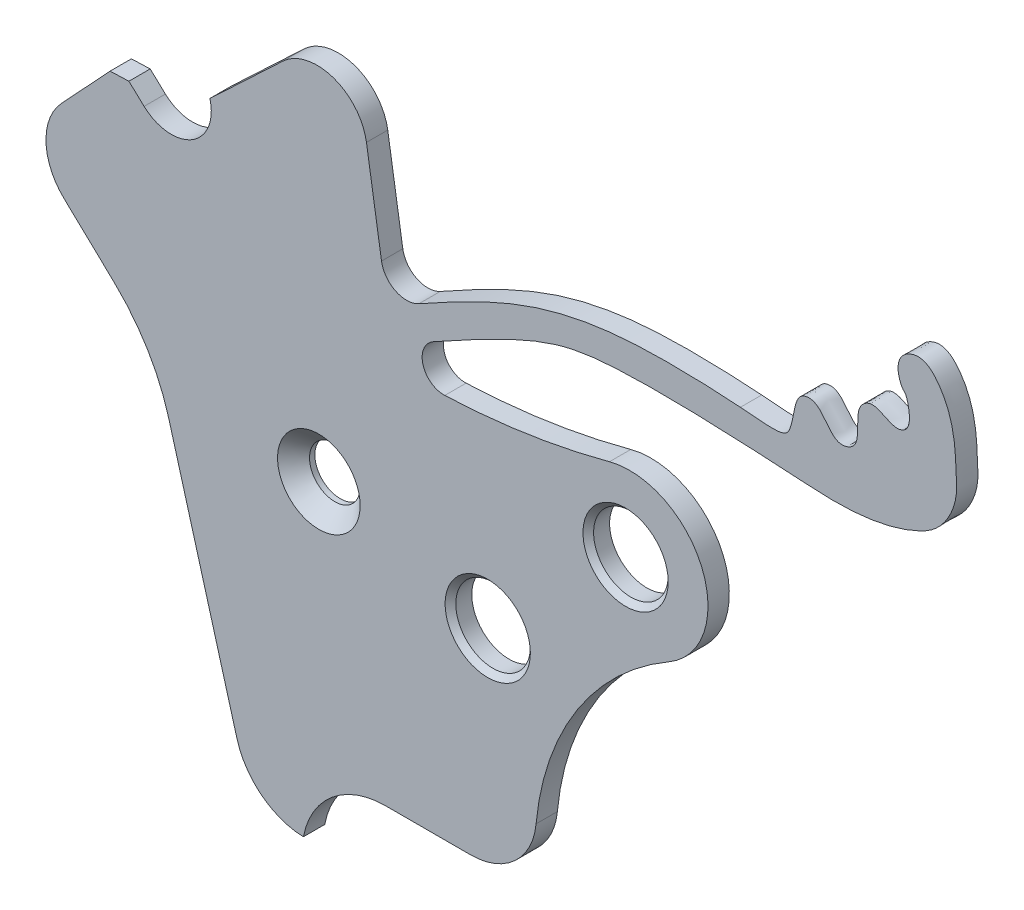
SolidWorks part; units mm, degrees
ref_plane "Alzado" through (0, 0, 0) normal (0, 0, 1) x (1, 0, 0)
ref_plane "Planta" through (0, 0, 0) normal (0, 1, 0) x (1, 0, 0)
ref_plane "Vista lateral" through (0, 0, 0) normal (1, 0, 0) x (0, 0, -1)
sketch "Sketch2" plane through (0, 0, 0) normal (0, 0, 1) x (1, 0, 0)
  line L0 (0, -1000) -> (0, 49000) construction
  line L1 (-1000, 0) -> (49000, 0) construction
  line L2 (-998.747, -6.2132) -> (49001.253, -6.2132) construction
  line L3 (-1000.2508, -4.5823) -> (48999.7492, -4.5823) construction
  line L4 (-0.2508, -1004.5823) -> (-0.2508, 48995.4177) construction
  line L5 (1.253, -1006.2132) -> (1.253, 48993.7868) construction
  line L6 (-997.1509, -3.408) -> (49002.8491, -3.408) construction
  line L7 (2.8491, -1003.408) -> (2.8491, 48996.592) construction
  line L8 (7.9138, -994.8329) -> (7.9138, 49005.1671) construction
  line L9 (10.9761, -993.0245) -> (10.9761, 49006.9755) construction
  line L10 (-992.0862, 5.1671) -> (49007.9138, 5.1671) construction
  line L11 (-989.0239, 6.9755) -> (49010.9761, 6.9755) construction
  line L16 (-3.2804, 4.4627) -> (-3.566, 4.7286)
  line L17 (-3.566, 4.7286) -> (-3.9193, 4.716)
  line L18 (-3.9193, 4.716) -> (-4.833, 3.7345)
  line L19 (-4.7853, 2.2137) -> (-3.8427, 1.3207)
  line L20 (-2.818, -0.3775) -> (-1.5375, -4.9432)
  line L21 (1.253, -4.6423) -> (2.8491, -4.6423)
  line L22 (1.1765, 4.1761) -> (0.8938, 5.9641)
  line L23 (-0.6755, 6.5) -> (-2.0457, 5.2086)
  line L24 (-990.9192, -3.9957) -> (49009.0808, -3.9957) construction
  line L25 (9.0808, -1003.9957) -> (9.0808, 48996.0043) construction
  line L26 (-6.4045, -1001.3833) -> (-6.4045, 48998.6167) construction
  line L27 (-4.042, -997.0018) -> (-4.042, 49002.9982) construction
  line L28 (-2.7694, -994.9883) -> (-2.7694, 49005.0117) construction
  line L29 (-1002.7694, 5.0117) -> (48997.2306, 5.0117) construction
  line L30 (0, 0) -> (36385.3008, 34294.4586) construction
  line L31 (0, 0) -> (-7808.4045, 49386.5247) construction
  line L32 (5.8347, -998.3687) -> (5.8347, 49001.6313) construction
  line L33 (1.6476, -995.7494) -> (1.6476, 49004.2506) construction
  line L34 (2.3481, -997.0064) -> (2.3481, 49002.9936) construction
  line L35 (-998.3524, 4.2506) -> (49001.6476, 4.2506) construction
  line L36 (-997.6519, 2.9936) -> (49002.3481, 2.9936) construction
  arc A24 (-4.833, 3.7345) -> (-4.7853, 2.2137) centre (-4.042, 2.9982) ccw
  arc A25 (-2.818, -0.3775) -> (-3.8427, 1.3207) centre (-6.4045, -1.3833) ccw
  arc A26 (-1.5375, -4.9432) -> (-0.29, -5.9182) centre (-0.2508, -4.5823) ccw
  arc A27 (1.253, -4.6423) -> (-0.29, -5.9182) centre (1.253, -6.2132) ccw
  arc A28 (2.8491, -4.6423) -> (4.0779, -3.5239) centre (2.8491, -3.408) ccw
  arc A29 (6.5698, 0.357) -> (4.0779, -3.5239) centre (9.0808, -3.9957) ccw
  arc A30 (6.5698, 0.357) -> (5.4555, 3.0526) centre (5.8347, 1.6313) ccw
  arc A31 (2.3643, 2.5849) -> (5.4555, 3.0526) centre (1.8036, 16.74) ccw
  arc A32 (2.1489, 3.351) -> (2.3643, 2.5849) centre (2.3481, 2.9936) ccw
  arc A33 (1.1765, 4.1761) -> (1.8798, 3.834) centre (1.6476, 4.2506) ccw
  arc A34 (0.8938, 5.9641) -> (-0.6755, 6.5) centre (-0.0324, 5.8177) ccw
  arc A35 (-3.2804, 4.4627) -> (-2.0457, 5.2086) centre (-2.7694, 5.0117) ccw
  spline S6 degree 3 poles (2.1489, 3.351) (3.9908, 4.3775) (5.0546, 4.7498) (8.0774, 4.611) (9.9748, 4.4876) (10.8761, 4.6128) (11.7359, 5.0825) (12.0069, 5.63) (11.9646, 6.0886) (11.9479, 6.5828) (11.873, 7.1699) (11.4017, 7.6985) (11.1184, 7.642) (10.7541, 7.4331) (10.9075, 7.0458) (10.9761, 6.9755) knots 0 0 0 0 0.257494 0.509772 0.556127 0.672708 0.696759 0.76611 0.785364 0.796026 0.872722 0.911006 0.922367 0.931267 1 1 1 1
  spline S7 degree 3 poles (10.9761, 6.9755) (11.0072, 6.9435) (11.031, 6.9271) (11.1835, 6.4366) (10.7681, 6.2108) (10.4744, 6.5466) (9.9858, 6.2373) (10.2614, 5.6336) (9.6011, 5.4168) (9.462, 5.9988) (8.9539, 5.9419) (8.933, 5.6159) (8.804, 5.0999) (8.7665, 5.0918) (7.9138, 5.1671) knots 0 0 0 0 0.010451 0.122621 0.153759 0.268567 0.304391 0.463925 0.508356 0.652283 0.681879 0.784526 0.80005 1 1 1 1
  spline S8 degree 3 poles (7.9138, 5.1671) (7.6138, 5.1935) (4.7791, 5.3381) (3.3615, 4.6598) (1.8798, 3.834) knots 0 0 0 0 0.292259 1 1 1 1
  dimension "D6" = 2.7694
  dimension "D7" = 4.042
  dimension "D10" = 1.6476
  dimension "D11" = 2.3481
  dimension "D16" = 4.2506
  dimension "D20" = 4.5823
  dimension "D22" = 1.3364
  dimension "D27" = 3.7249
  dimension "D30" = 43.306
  dimension "D32" = 0.3533
  dimension "D37" = 0.4769
  dimension "D38" = 0.4091
  dimension "D23" = 1.5709
  dimension "D24" = 1.2343
  dimension "D25" = 5.0251
  dimension "D26" = 1.471
  dimension "D28" = 1.0806
  dimension "D31" = 0.75
  dimension "D36" = 0.9377
  dimension "D39" = 14.1663
  dimension "D2" = 8.985
  dimension "D3" = 43.453
  dimension "D4" = 15.666
  dimension "D5" = 0.2508
  dimension "D8" = 6.4045
  dimension "D9" = 1.253
  dimension "D12" = 2.8491
  dimension "D13" = 5.8347
  dimension "D14" = 9.0808
  dimension "D15" = 2.9936
  dimension "D17" = 5.0117
  dimension "D18" = 3.408
  dimension "D19" = 3.9957
  dimension "D21" = 6.2132
  dimension "D29" = 47.048
  dimension "D33" = 45
  dimension "D34" = 1.8142
  dimension "D35" = 5.1935
  dimension "D1" = 43.306
  dimension "D40" = 5.1671
  dimension "D41" = 6.9755
  dimension "D42" = 7.9138
  dimension "D43" = 10.9761
extrude "Boss-Extrude1" add sketch "Sketch2" along normal blind 0.4
sketch "Sketch3" plane through (0, 0, 0) normal (0, 0, 1) x (1, 0, 0)
  line L0 (0, -1000) -> (0, 49000) construction
  line L1 (3.171, -999.6826) -> (3.171, 49000.3174) construction
  line L2 (3.171, -0.8) -> (36294.8338, 34392.7345) construction
  line L3 (-1000, 0) -> (49000, 0) construction
  line L4 (3.171, -0.8) -> (-48476.2149, 12236.4031) construction
  line L5 (-999.255, -0.8) -> (49000.745, -0.8) construction
  line L6 (-2.7699, 5.0122) -> (35737.5231, -34961.1351) construction
  circle A0 centre (3.171, -0.8) radius 8.3105 construction
  circle A1 centre (3.171, -0.8) radius 0.7
  circle A2 centre (3.171, -0.8) radius 3.565 construction
  arc A3 (-3.2804, 4.4627) -> (-2.0457, 5.2086) centre (-2.7694, 5.0117) ccw construction
  arc A4 (-3.2804, 4.4627) -> (-2.0457, 5.2086) centre (-2.7694, 5.0117) ccw construction
  circle A5 centre (3.171, -0.8) radius 3.2707 construction
  circle A6 centre (0, 0) radius 0.475
  circle A7 centre (5.7586, 1.6522) radius 0.7
  point P11 (5.7586, 1.6522)
  point P12 (3.171, -0.8)
  point P20 (-0.0002, 0.0005)
  dimension "D5" = 6.5414
  dimension "D6" = 1.4
  dimension "D7" = 92.166
  dimension "D2" = 16.6209
  dimension "D3" = 7.1299
  dimension "D9" = 0.95
  dimension "D10" = 1.4
  dimension "D1" = 3.171
  dimension "D4" = 0.8
  dimension "D8" = 30.206
extrude "Cut-Extrude1" cut sketch "Sketch3" along normal up to next
chamfer "Chamfer1" distance 0.3 angle 45 1 edges at (0.475, 0, 0.4)
chamfer "Chamfer2" distance 0.1 angle 45 2 edges at (3.871, -0.8, 0.4) (6.4586, 1.6522, 0.4)
